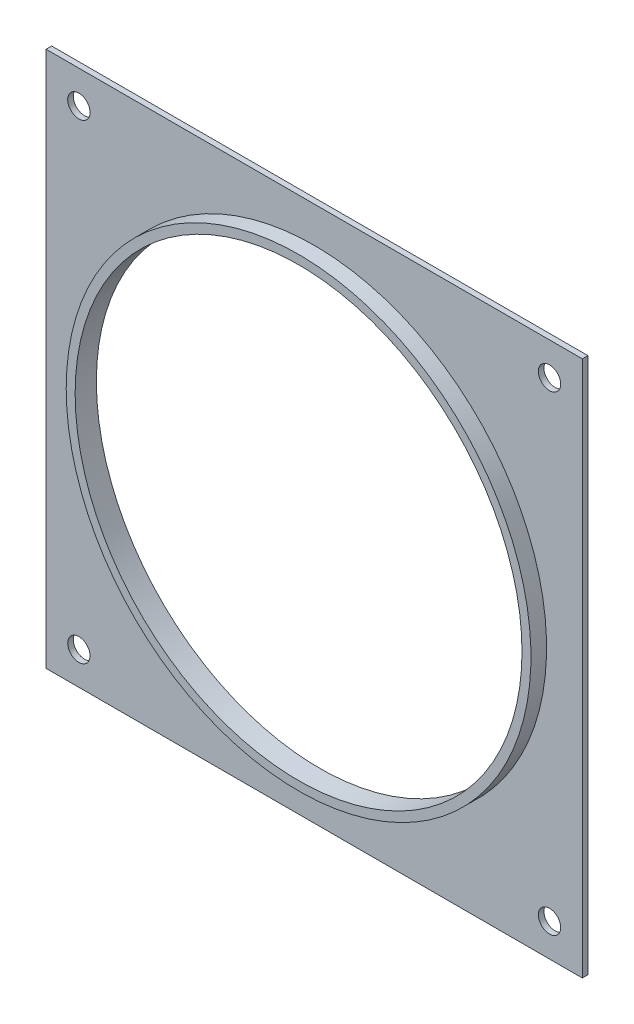
SolidWorks part; units mm, degrees
material "Alloy Steel"
ref_plane "Front Plane" through (0, 0, 0) normal (0, 0, 1) x (1, 0, 0)
ref_plane "Top Plane" through (0, 0, 0) normal (0, 1, 0) x (1, 0, 0)
ref_plane "Right Plane" through (0, 0, 0) normal (1, 0, 0) x (0, 0, -1)
sketch "Sketch1" plane through (0, 0, 0) normal (0, 0, 1) x (1, 0, 0)
  line L0 (0, 0) -> (0, 89.8417) construction
  line L1 (0, 0) -> (85.093, 0) construction
  line L2 (-76.2, 76.2) -> (76.2, 76.2)
  line L3 (76.2, 76.2) -> (76.2, -76.2)
  line L4 (-76.2, 76.2) -> (-76.2, -76.2)
  line L5 (-76.2, -76.2) -> (76.2, -76.2)
  circle A0 centre (0, 0) radius 63.5
  point P10 (0, 76.2)
  point P11 (-76.2, 0)
  point P12 (76.2, 0)
  dimension "D1" = 127
  dimension "D2" = 152.4
  dimension "D3" = 152.4
extrude "Boss-Extrude1" add sketch "Sketch1" along normal blind 1.5875
sketch "Sketch2" plane through (0, 0, 1.5875) normal (0, 0, 1) x (1, 0, 0)
  circle A0 centre (0, 0) radius 66.04
  circle A1 centre (0, 0) radius 63.5 construction
  circle A2 centre (0, 0) radius 63.5
  dimension "D1" = 2.54
extrude "Boss-Extrude2" add sketch "Sketch2" along normal offset from surface (4.445 mm away) 6.0325 up to face at (0, 0, 0)
sketch "Sketch3" plane through (0, 0, 1.5875) normal (0, 0, 1) x (1, 0, 0)
  line L0 (0, 0) -> (0, -106.5116) construction
  line L1 (0, 0) -> (138.2793, 0) construction
  line L4 (76.2, -76.2) -> (76.2, 76.2) construction
  line L5 (-76.2, -76.2) -> (76.2, -76.2) construction
  circle A0 centre (66.8782, -66.8782) radius 3.175
  circle A1 centre (-66.8782, -66.8782) radius 3.175
  circle A2 centre (-66.8782, 66.8782) radius 3.175
  circle A3 centre (66.8782, 66.8782) radius 3.175
  dimension "D3" = 6.35
  dimension "D1" = 9.3218
  dimension "D2" = 9.3218
extrude "Cut-Extrude1" cut sketch "Sketch3" against normal up to surface (1.5875 mm away) up to face at (0, 0, 0)
